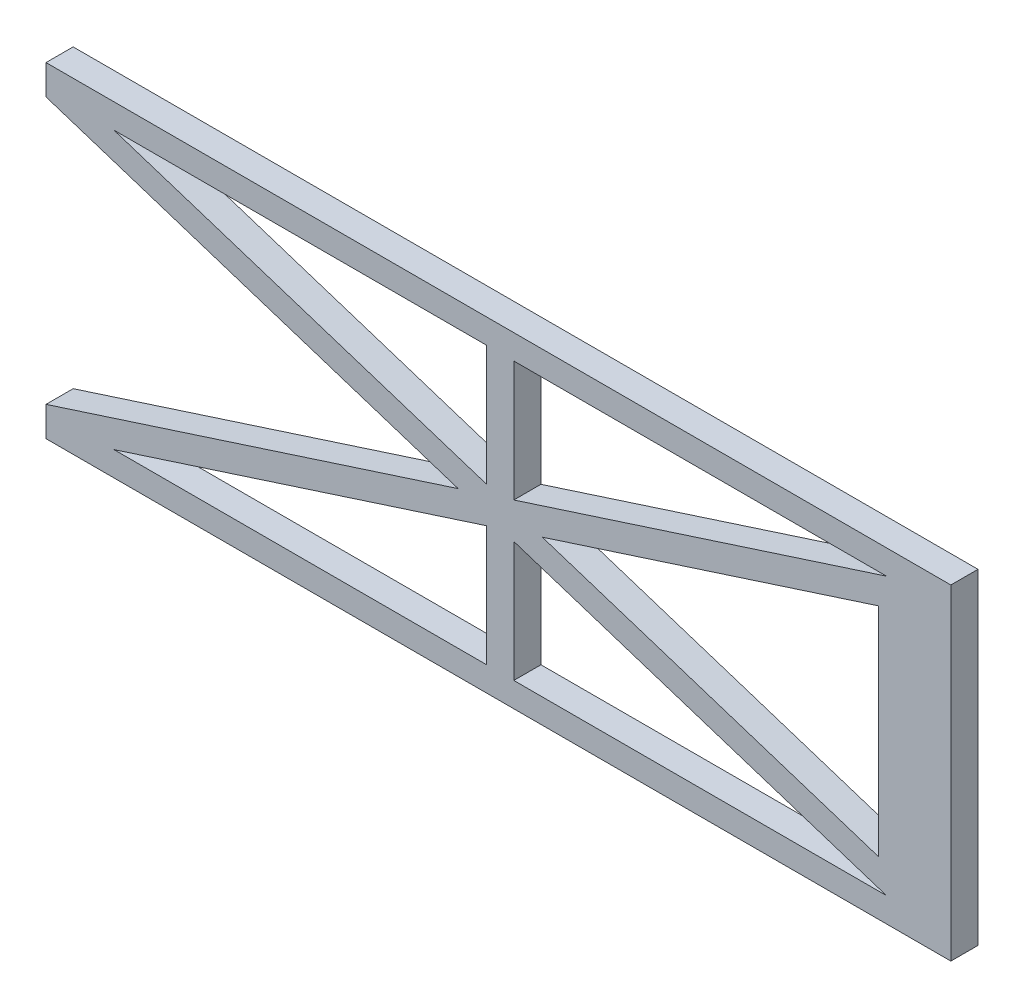
SolidWorks part; units mm, degrees
material "AISI 1020"
ref_plane "Front Plane" through (0, 0, 0) normal (0, 0, 1) x (1, 0, 0)
ref_plane "Top Plane" through (0, 0, 0) normal (0, 1, 0) x (1, 0, 0)
ref_plane "Right Plane" through (0, 0, 0) normal (1, 0, 0) x (0, 0, -1)
sketch "Sketch2" plane through (0, 0, 0) normal (0, 0, 1) x (1, 0, 0)
  line L0 (0, 0) -> (-928.9153, 0)
  line L1 (-928.9153, 0) -> (-928.9153, 27.1207)
  line L2 (-928.9153, 27.1207) -> (71.0847, 27.1207)
  line L3 (71.0847, 27.1207) -> (71.0847, -32.8793)
  line L4 (71.0847, -32.8793) -> (-8.9153, -32.8793)
  line L5 (-8.9153, -32.8793) -> (-928.9153, -330)
  line L6 (-928.9153, -330) -> (-928.9153, -300)
  line L7 (-928.9153, -300) -> (0, 0)
  dimension "D1" = 60
  dimension "D2" = 1000
  dimension "D3" = 27.1207
  dimension "D4" = 30
  dimension "D5" = 80
  dimension "D6" = 300
extrude "Original Truss Part" add sketch "Sketch2" against normal blind 30
ref_plane "Plane1" through (0, -152.8793, 0) normal (0, 1, 0) x (1, 0, 0)
mirror "OG Part Mirror" about plane through (0, -152.8793, 0) normal (0, 1, 0) of "Original Truss Part"
sketch "Sketch14" plane through (0, -305.7585, 0) normal (0, 1, 0) x (1, 0, 0)
  line L0 (-853.8544, 0) -> (0, 0) construction
  line L1 (-441.9272, 0) -> (-411.9272, 0)
  line L2 (-441.9272, 0) -> (-441.9272, 30)
  line L3 (-441.9272, 30) -> (-411.9272, 30)
  line L4 (-411.9272, 0) -> (-411.9272, 30)
  line L5 (-853.8544, 30) -> (0, 30) construction
  point P8 (-426.9272, 0)
  point P9 (-426.9272, 0)
extrude "Center Support" add sketch "Sketch14" along normal up to surface (305.7585 mm away) up to face at (-426.9272, 0, -15)
sketch "Sketch15" plane through (0, -272.8793, 0) normal (0, 1, 0) x (1, 0, 0)
  line L1 (-8.9153, 30) -> (71.0847, 30)
  line L2 (-8.9153, 30) -> (-8.9153, 0)
  line L3 (-8.9153, 0) -> (71.0847, 0)
  line L4 (71.0847, 30) -> (71.0847, 0)
extrude "Right Support" add sketch "Sketch15" along normal up to next
